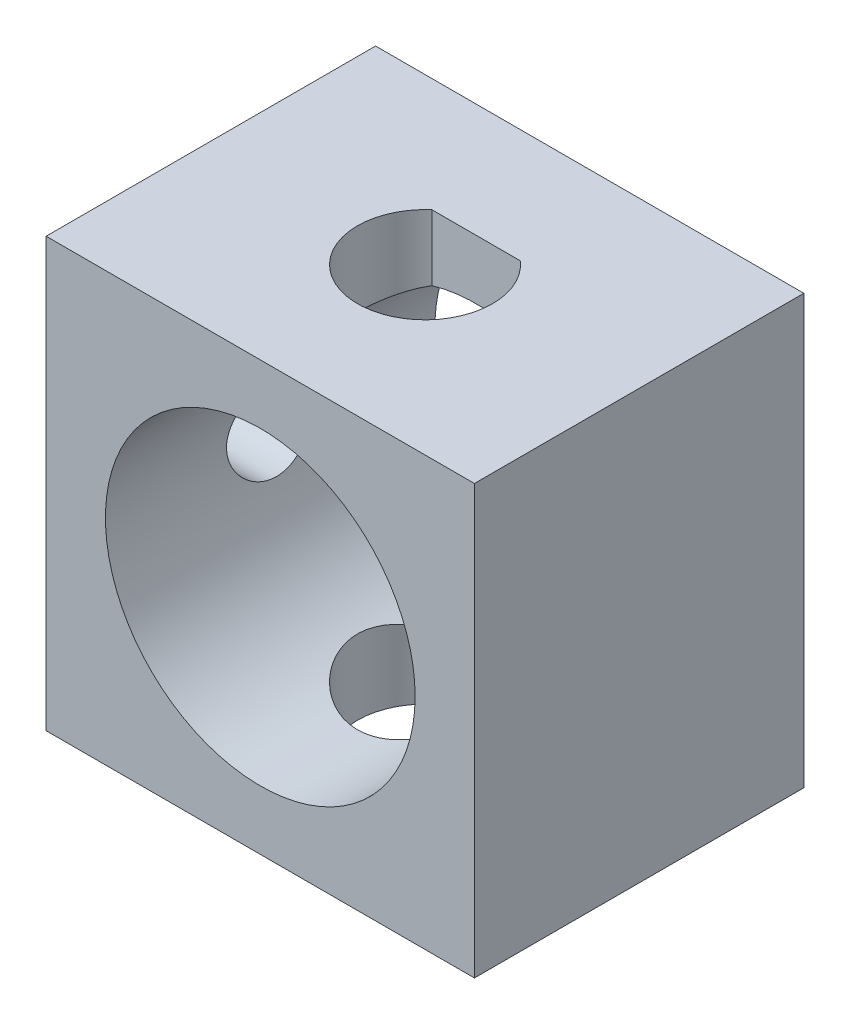
SolidWorks part; units mm, degrees
ref_plane "Front Plane" through (0, 0, 0) normal (0, 0, 1) x (1, 0, 0)
ref_plane "Top Plane" through (0, 0, 0) normal (0, 1, 0) x (1, 0, 0)
ref_plane "Right Plane" through (0, 0, 0) normal (1, 0, 0) x (0, 0, -1)
sketch "Sketch1" plane through (0, 0, 0) normal (0, 1, 0) x (1, 0, 0)
  line L0 (-1.3416, 1.55) -> (1.3416, 1.55)
  line L1 (-6.5, -5) -> (6.5, -5)
  line L2 (-6.5, -5) -> (-6.5, 5)
  line L3 (-6.5, 5) -> (6.5, 5)
  line L4 (6.5, -5) -> (6.5, 5)
  line L5 (-6.5, -5) -> (6.5, 5) construction
  line L6 (-6.5, 5) -> (6.5, -5) construction
  circle A0 centre (0, 0) radius 2.05
  point P0 (0, 0)
  dimension "D3" = 4.1
  dimension "D1" = 13
  dimension "D2" = 10
  dimension "D4" = 0.5
extrude "Boss-Extrude1" add sketch "Sketch1" along normal blind 13 contours L1 L4 L3 L2 A0 | L0 A0
sketch "Sketch2" plane through (0, 0, 5) normal (0, 0, 1) x (1, 0, 0)
  line L0 (-6.5, 13) -> (-6.5, 0) construction
  circle A0 centre (0, 6.5) radius 4.7
  point P5 (-6.5, 6.5)
  point P8 (0, 0)
  point P9 (0, 0)
  point P10 (0, 0)
  point P12 (0, 6.5)
  dimension "D1" = 9.4
extrude "Cut-Extrude1" cut sketch "Sketch2" against normal blind 10
sketch "Sketch3" plane through (-6.5, 0, 0) normal (-1, 0, 0) x (0, 0, 1)
  line L0 (5, 13) -> (5, 0) construction
  circle A0 centre (0, 6.5) radius 1.325
  point P2 (0, 0)
  point P6 (5, 6.5)
  dimension "D1" = 2.65
extrude "Cut-Extrude2" cut sketch "Sketch3" against normal up to next
